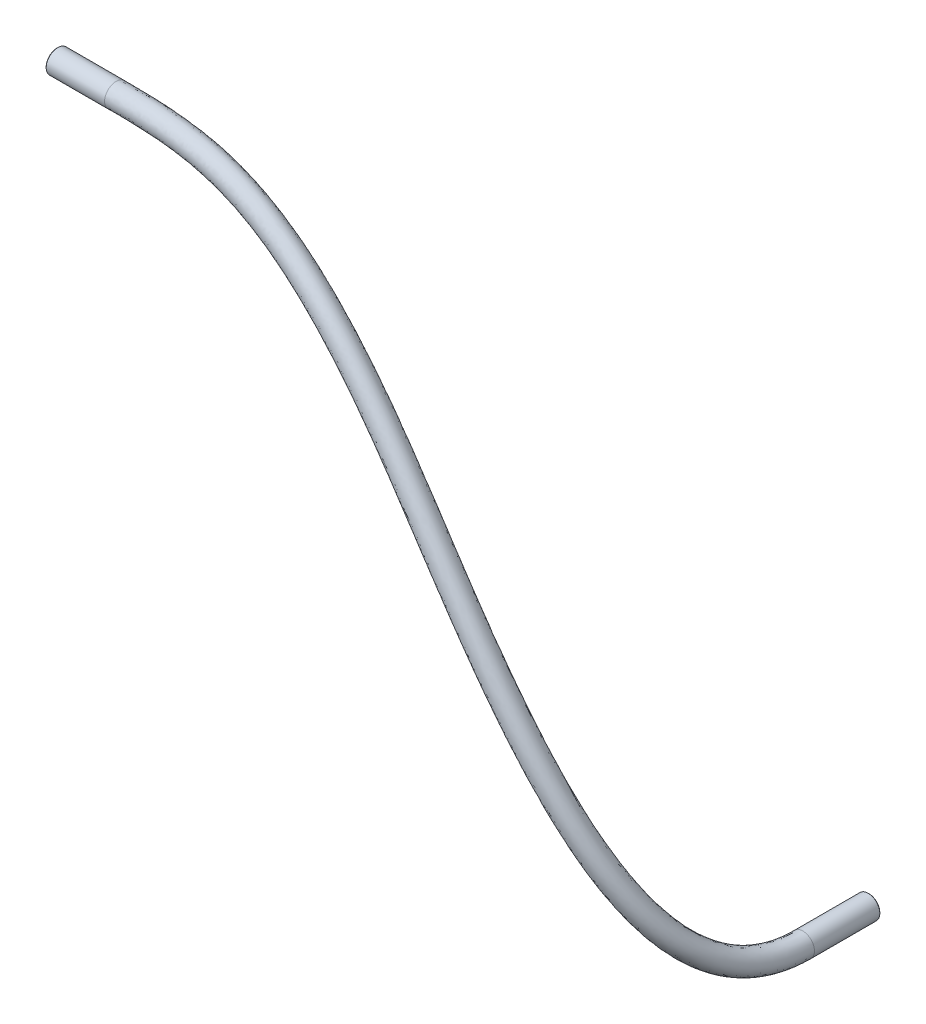
SolidWorks part; units mm, degrees
ref_plane "Front Plane" through (0, 0, 0) normal (0, 0, 1) x (1, 0, 0)
ref_plane "Top Plane" through (0, 0, 0) normal (0, 1, 0) x (1, 0, 0)
ref_plane "Right Plane" through (0, 0, 0) normal (1, 0, 0) x (0, 0, -1)
sketch3d "3DSketch1"
  line L0 (201.3105, -198.3536, -49.6875) -> (201.3105, -198.3536, -61.0875)
  line L1 (96.825, -106.4823, -25.525) -> (107.025, -106.4823, -25.525)
  spline S0 degree 3 poles (107.025, -106.4823, -25.525) (123.3099, -106.4823, -25.525) (146.4598, -109.9657, -26.2048) (201.3105, -198.3536, -18.6951) (201.3105, -198.3536, -49.6875) knots 0 0 0 0 0.513706 1 1 1 1
sketch "Sketch1" plane through (104.925, 0, 0) normal (1, 0, 0) x (0, 0, -1)
  circle A0 centre (25.525, -106.4823) radius 2
  circle A1 centre (25.525, -106.4823) radius 1.3
  circle A3 centre (25.525, -106.4823) radius 3.5 construction
  dimension "D1" = 4
  dimension "D2" = 2.6
sweep "Sweep1" add profiles "Sketch1" path "3DSketch1"
chamfer "Chamfer1" distance 0.127 angle 45 4 edges at (203.2018, -197.7031, -61.0875) (202.5398, -197.9308, -61.0875) (96.825, -104.4823, -25.525) (96.825, -105.1823, -25.525)
